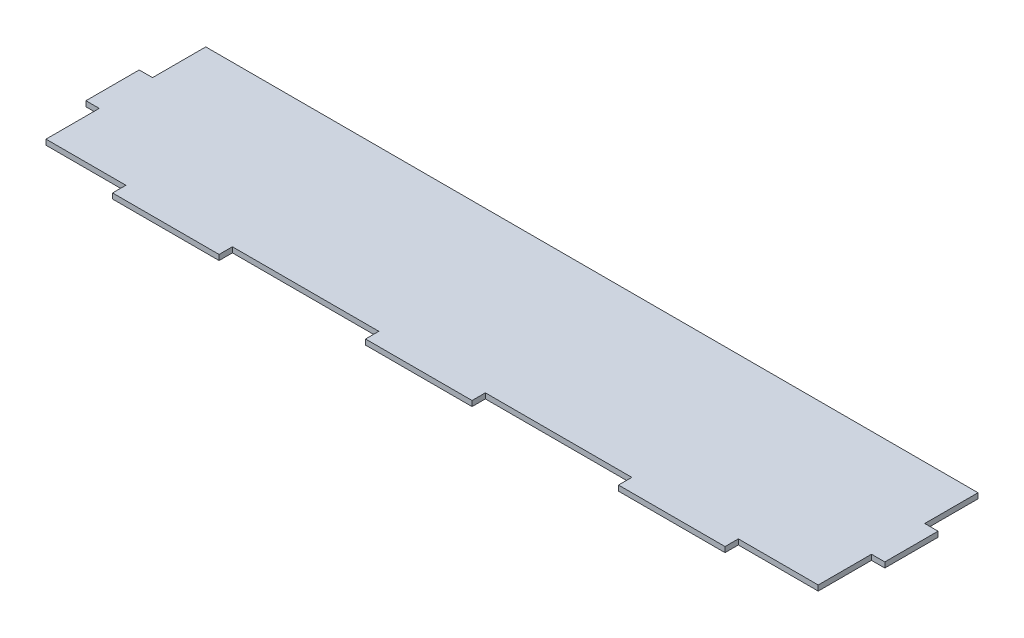
SolidWorks part; units mm, degrees
ref_plane "Front Plane" through (0, 0, 0) normal (0, 0, 1) x (1, 0, 0)
ref_plane "Top Plane" through (0, 0, 0) normal (0, 1, 0) x (1, 0, 0)
ref_plane "Right Plane" through (0, 0, 0) normal (1, 0, 0) x (0, 0, -1)
sketch "Sketch1" plane through (0, 0, 0) normal (0, 1, 0) x (1, 0, 0)
  line L0 (0, 12.434) -> (0, -12.966)
  line L1 (6.35, 37.834) -> (374.65, 37.834)
  line L2 (381, 12.434) -> (381, -12.966)
  line L3 (6.35, -38.366) -> (44.45, -38.366)
  line L4 (95.25, -38.366) -> (165.1, -38.366)
  line L5 (165.1, -38.366) -> (165.105, -38.311)
  line L7 (0, 12.434) -> (6.35, 12.434)
  line L8 (6.35, 37.834) -> (6.35, 12.434)
  line L9 (44.45, -38.366) -> (44.45, -44.716)
  line L11 (0, -12.966) -> (6.35, -12.966)
  line L12 (6.35, -38.366) -> (6.35, -12.966)
  line L14 (381, 12.434) -> (374.65, 12.434)
  line L15 (374.65, 37.834) -> (374.65, 12.434)
  line L16 (44.45, -44.716) -> (95.25, -44.716)
  line L17 (95.25, -38.366) -> (95.25, -44.716)
  line L18 (381, -12.966) -> (374.65, -12.966)
  line L19 (374.65, -38.366) -> (374.65, -12.966)
  line L20 (215.9, -38.366) -> (285.75, -38.366)
  line L21 (336.55, -38.366) -> (336.55, -44.716)
  line L22 (336.55, -44.716) -> (285.75, -44.716)
  line L23 (285.75, -38.366) -> (285.75, -44.716)
  line L24 (336.55, -38.366) -> (374.65, -38.366)
  line L25 (165.1, -38.366) -> (165.1, -44.716)
  line L26 (165.1, -44.716) -> (215.9, -44.716)
  line L27 (215.9, -38.366) -> (215.9, -44.716)
  dimension "D2" = 368.3
  dimension "D3" = 25.4
  dimension "D4" = 25.4
  dimension "D5" = 6.35
  dimension "D6" = 6.35
  dimension "D7" = 25.4
  dimension "D8" = 25.4
  dimension "D9" = 25.4
  dimension "D10" = 6.35
  dimension "D11" = 6.35
  dimension "D12" = 6.35
  dimension "D13" = 368.3
  dimension "D14" = 6.35
  dimension "D15" = 25.4
  dimension "D16" = 25.4
  dimension "D17" = 25.4
  dimension "D18" = 25.4
  dimension "D19" = 25.4
  dimension "D20" = 50.8
  dimension "D21" = 25.4
  dimension "D22" = 69.85
  dimension "D23" = 6.35
  dimension "D24" = 50.8
  dimension "D25" = 44.45
  dimension "D26" = 6.35
  dimension "D27" = 50.8
  dimension "D28" = 44.45
  dimension "D29" = 6.35
  dimension "D30" = 50.8
  dimension "D31" = 69.85
  dimension "D32" = 69.85
  dimension "D33" = 50.8
  dimension "D34" = 50.8
  dimension "D35" = 38.1
  dimension "D36" = 6.35
  dimension "D37" = 6.35
  dimension "D38" = 6.35
  dimension "D39" = 6.35
extrude "Boss-Extrude1" add sketch "Sketch1" along normal blind 2.54
